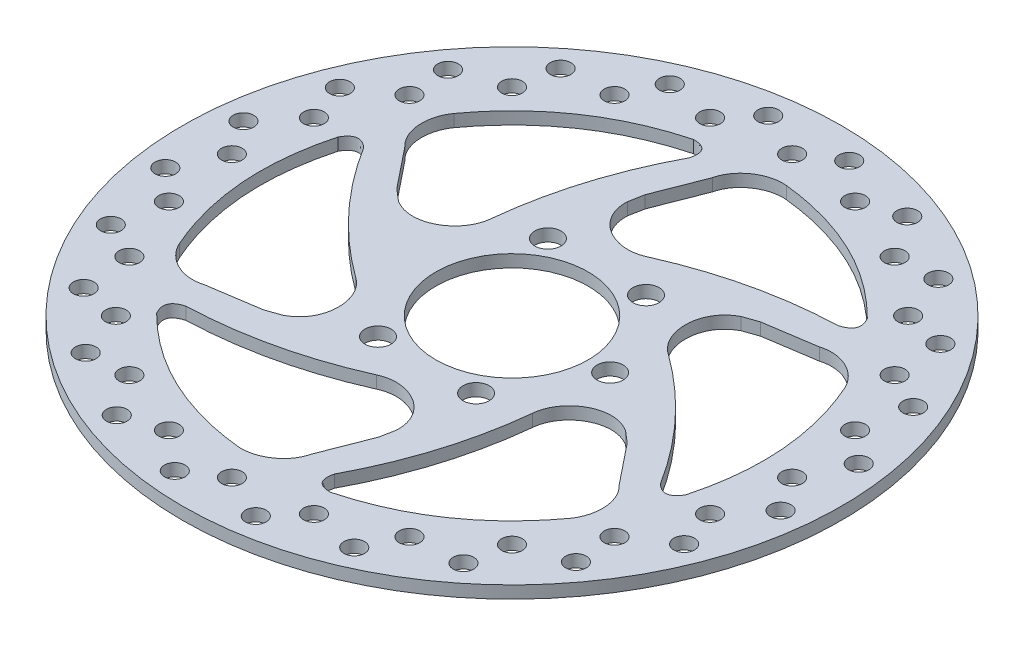
SolidWorks part; units mm, degrees
ref_plane "Front Plane" through (0, 0, 0) normal (0, 0, 1) x (1, 0, 0)
ref_plane "Top Plane" through (0, 0, 0) normal (0, 1, 0) x (1, 0, 0)
ref_plane "Right Plane" through (0, 0, 0) normal (1, 0, 0) x (0, 0, -1)
sketch "Sketch1" plane through (0, 0, 0) normal (0, 1, 0) x (1, 0, 0)
  line L0 (-9.316, 41.6349) -> (-4.7427, 53.3559)
  line L1 (31.3989, 28.8853) -> (43.8362, 30.7853)
  line L2 (40.7149, -12.7495) -> (48.5789, -22.5706)
  line L3 (9.316, -41.6349) -> (4.7427, -53.3559)
  line L4 (-31.3989, -28.8853) -> (-43.8362, -30.7853)
  line L5 (-40.7149, 12.7495) -> (-48.5789, 22.5706)
  circle A0 centre (0, 0) radius 80
  circle A1 centre (0, 68) radius 2.5
  circle A2 centre (8.3322, 73.5294) radius 2.5
  circle A3 centre (17.5997, 65.683) radius 2.5
  circle A4 centre (27.0791, 68.8674) radius 2.5
  circle A5 centre (34, 58.8897) radius 2.5
  circle A6 centre (43.9806, 59.5122) radius 2.5
  circle A7 centre (48.0833, 48.0833) radius 2.5
  circle A8 centre (57.8849, 46.1014) radius 2.5
  circle A9 centre (58.8897, 34) radius 2.5
  circle A10 centre (67.8444, 29.5488) radius 2.5
  circle A11 centre (65.683, 17.5997) radius 2.5
  circle A12 centre (73.1805, 10.9825) radius 2.5
  circle A13 centre (68, 0) radius 2.5
  circle A14 centre (73.5294, -8.3322) radius 2.5
  circle A15 centre (65.683, -17.5997) radius 2.5
  circle A16 centre (68.8674, -27.0791) radius 2.5
  circle A17 centre (58.8897, -34) radius 2.5
  circle A18 centre (59.5122, -43.9806) radius 2.5
  circle A19 centre (48.0833, -48.0833) radius 2.5
  circle A20 centre (46.1014, -57.8849) radius 2.5
  circle A21 centre (34, -58.8897) radius 2.5
  circle A22 centre (29.5488, -67.8444) radius 2.5
  circle A23 centre (17.5997, -65.683) radius 2.5
  circle A24 centre (10.9825, -73.1805) radius 2.5
  circle A25 centre (0, -68) radius 2.5
  circle A26 centre (-8.3322, -73.5294) radius 2.5
  circle A27 centre (-17.5997, -65.683) radius 2.5
  circle A28 centre (-27.0791, -68.8674) radius 2.5
  circle A29 centre (-34, -58.8897) radius 2.5
  circle A30 centre (-43.9806, -59.5122) radius 2.5
  circle A31 centre (-48.0833, -48.0833) radius 2.5
  circle A32 centre (-57.8849, -46.1014) radius 2.5
  circle A33 centre (-58.8897, -34) radius 2.5
  circle A34 centre (-67.8444, -29.5488) radius 2.5
  circle A35 centre (-65.683, -17.5997) radius 2.5
  circle A36 centre (-73.1805, -10.9825) radius 2.5
  circle A37 centre (-68, 0) radius 2.5
  circle A38 centre (-73.5294, 8.3322) radius 2.5
  circle A39 centre (-65.683, 17.5997) radius 2.5
  circle A40 centre (-68.8674, 27.0791) radius 2.5
  circle A41 centre (-58.8897, 34) radius 2.5
  circle A42 centre (-59.5122, 43.9806) radius 2.5
  circle A43 centre (-48.0833, 48.0833) radius 2.5
  circle A44 centre (-46.1014, 57.8849) radius 2.5
  circle A45 centre (-34, 58.8897) radius 2.5
  circle A46 centre (-29.5488, 67.8444) radius 2.5
  circle A47 centre (-17.5997, 65.683) radius 2.5
  circle A48 centre (-10.9825, 73.1805) radius 2.5
  circle A49 centre (0, 0) radius 18.5
  circle A50 centre (-11.9063, 20.6222) radius 3.175
  circle A51 centre (11.9063, 20.6222) radius 3.175
  circle A52 centre (23.8125, 0) radius 3.175
  circle A53 centre (11.9063, -20.6222) radius 3.175
  circle A54 centre (-11.9063, -20.6222) radius 3.175
  spline S0 degree 2 poles (5.9532, 60.7088) (27.9941, 58.3228) (43.6425, 42.6185) knots 0 0 0 1 1 1
  spline S1 degree 2 poles (4.0813, 28.8708) (21.9975, 36.8421) (41.5951, 37.5241) knots 0 0 0 1 1 1
  spline S2 degree 1 poles (-10, 38) (-9.316, 41.6349) knots 0 0 1 1
  spline S3 degree 3 poles (-4.7427, 53.3559) (-3.6172, 58.1411) (1.3644, 61.1789) (5.9532, 60.7088) knots 0 0 0 0 1 1 1 1
  spline S4 degree 3 poles (4.0813, 28.8708) (-1.8873, 26.0232) (-10.3042, 30.435) (-10, 38) knots 0 0 0 0 1 1 1 1
  spline S5 degree 2 poles (41.5951, 37.5241) (45.9407, 38.7363) (43.6425, 42.6185) knots 0 0 0 1 1 1
  spline S6 degree 2 poles (53.2944, -17.2603) (56.5169, -20.4176) (58.7299, -16.4862) knots 0 0 0 1 1 1
  spline S7 degree 2 poles (55.552, 25.1988) (64.506, 4.9178) (58.7299, -16.4862) knots 0 0 0 1 1 1
  spline S8 degree 3 poles (43.8362, 30.7853) (48.5431, 32.2031) (53.6647, 29.4078) (55.552, 25.1988) knots 0 0 0 0 1 1 1 1
  spline S9 degree 1 poles (27.909, 27.6603) (31.3989, 28.8853) knots 0 0 1 1
  spline S10 degree 3 poles (27.0435, 10.9008) (21.5931, 14.646) (21.2054, 24.1412) (27.909, 27.6603) knots 0 0 0 0 1 1 1 1
  spline S11 degree 2 poles (27.0435, 10.9008) (42.905, -0.6293) (53.2944, -17.2603) knots 0 0 0 1 1 1
  spline S12 degree 2 poles (11.6993, -54.7845) (10.5763, -59.1539) (15.0875, -59.1047) knots 0 0 0 1 1 1
  spline S13 degree 2 poles (49.5988, -35.51) (36.5119, -53.405) (15.0875, -59.1047) knots 0 0 0 1 1 1
  spline S14 degree 3 poles (48.5789, -22.5706) (52.1602, -25.938) (52.3003, -31.7711) (49.5988, -35.51) knots 0 0 0 0 1 1 1 1
  spline S15 degree 1 poles (37.909, -10.3397) (40.7149, -12.7495) knots 0 0 1 1
  spline S16 degree 3 poles (22.9622, -17.9699) (23.4804, -11.3771) (31.5096, -6.2938) (37.909, -10.3397) knots 0 0 0 0 1 1 1 1
  spline S17 degree 2 poles (22.9622, -17.9699) (20.9075, -37.4715) (11.6993, -54.7845) knots 0 0 0 1 1 1
  spline S18 degree 2 poles (-41.5951, -37.5241) (-45.9407, -38.7363) (-43.6425, -42.6185) knots 0 0 0 1 1 1
  spline S19 degree 2 poles (-5.9532, -60.7088) (-27.9941, -58.3228) (-43.6425, -42.6185) knots 0 0 0 1 1 1
  spline S20 degree 3 poles (4.7427, -53.3559) (3.6172, -58.1411) (-1.3644, -61.1789) (-5.9532, -60.7088) knots 0 0 0 0 1 1 1 1
  spline S21 degree 1 poles (10, -38) (9.316, -41.6349) knots 0 0 1 1
  spline S22 degree 3 poles (-4.0813, -28.8708) (1.8873, -26.0232) (10.3042, -30.435) (10, -38) knots 0 0 0 0 1 1 1 1
  spline S23 degree 2 poles (-4.0813, -28.8708) (-21.9975, -36.8421) (-41.5951, -37.5241) knots 0 0 0 1 1 1
  spline S24 degree 2 poles (-53.2944, 17.2603) (-56.5169, 20.4176) (-58.7299, 16.4862) knots 0 0 0 1 1 1
  spline S25 degree 2 poles (-55.552, -25.1988) (-64.506, -4.9178) (-58.7299, 16.4862) knots 0 0 0 1 1 1
  spline S26 degree 3 poles (-43.8362, -30.7853) (-48.5431, -32.2031) (-53.6647, -29.4078) (-55.552, -25.1988) knots 0 0 0 0 1 1 1 1
  spline S27 degree 1 poles (-27.909, -27.6603) (-31.3989, -28.8853) knots 0 0 1 1
  spline S28 degree 3 poles (-27.0435, -10.9008) (-21.5931, -14.646) (-21.2054, -24.1412) (-27.909, -27.6603) knots 0 0 0 0 1 1 1 1
  spline S29 degree 2 poles (-27.0435, -10.9008) (-42.905, 0.6293) (-53.2944, 17.2603) knots 0 0 0 1 1 1
  spline S30 degree 2 poles (-11.6993, 54.7845) (-10.5763, 59.1539) (-15.0875, 59.1047) knots 0 0 0 1 1 1
  spline S31 degree 2 poles (-49.5988, 35.51) (-36.5119, 53.405) (-15.0875, 59.1047) knots 0 0 0 1 1 1
  spline S32 degree 3 poles (-48.5789, 22.5706) (-52.1602, 25.938) (-52.3003, 31.7711) (-49.5988, 35.51) knots 0 0 0 0 1 1 1 1
  spline S33 degree 1 poles (-37.909, 10.3397) (-40.7149, 12.7495) knots 0 0 1 1
  spline S34 degree 3 poles (-22.9622, 17.9699) (-23.4804, 11.3771) (-31.5096, 6.2938) (-37.909, 10.3397) knots 0 0 0 0 1 1 1 1
  spline S35 degree 2 poles (-22.9622, 17.9699) (-20.9075, 37.4715) (-11.6993, 54.7845) knots 0 0 0 1 1 1
extrude "Boss-Extrude1" add sketch "Sketch1" along normal blind 3
